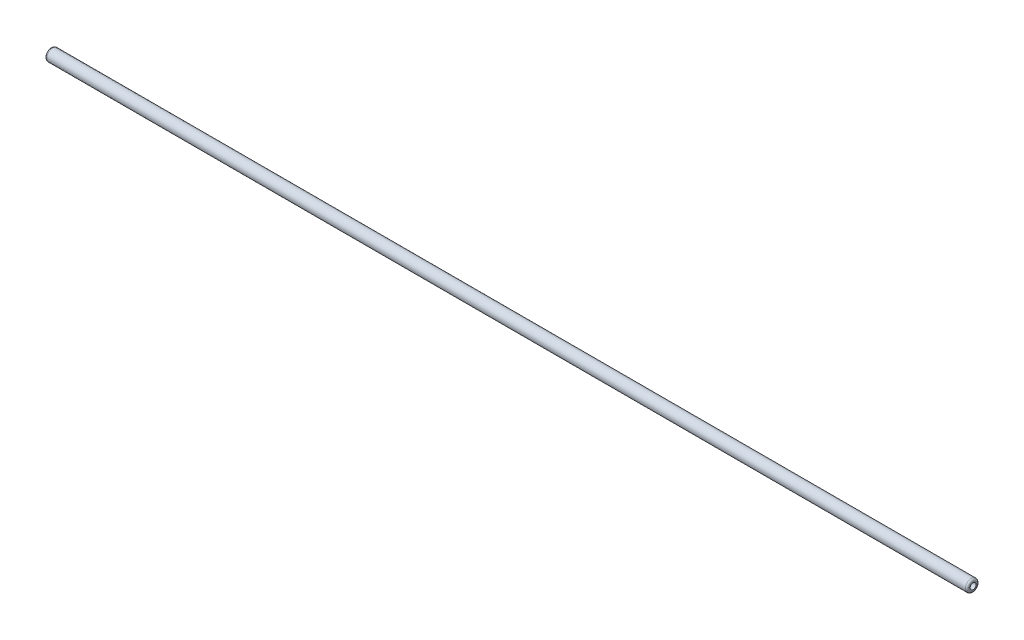
SolidWorks part; units mm, degrees
material "Alloy Steel"
ref_plane "Front Plane" through (0, 0, 0) normal (0, 0, 1) x (1, 0, 0)
ref_plane "Top Plane" through (0, 0, 0) normal (0, 1, 0) x (1, 0, 0)
ref_plane "Right Plane" through (0, 0, 0) normal (1, 0, 0) x (0, 0, -1)
sketch "스케치1" plane through (0, 0, 0) normal (0, 1, 0) x (1, 0, 0)
  circle A0 centre (0, 0) radius 7.9375
  circle A1 centre (0, 0) radius 3.975
  dimension "D1" = 15.875
  dimension "D2" = 7.95
extrude "보스-돌출1" add sketch "스케치1" along normal mid plane 1228.725
fillet "필렛1" radius 2.5 2 edges at (0, 614.3625, 7.9375) (0, -614.3625, 7.9375)
move or copy body "바디-이동/복사1" bodies to move or copy 101 copy no rotation origin (0, 0, 0) rotation axis (0, 0, 1) rotation angle 90
